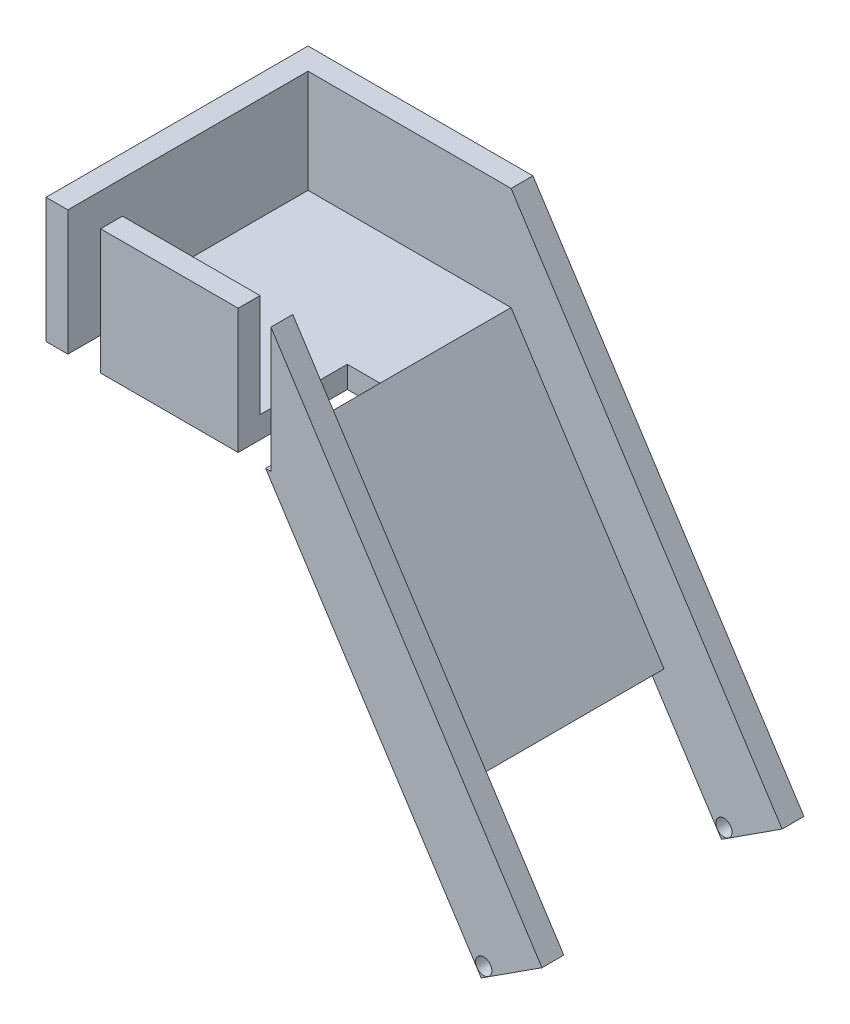
SolidWorks part; units mm, degrees
ref_plane "Plan de face" through (0, 0, 0) normal (0, 0, 1) x (1, 0, 0)
ref_plane "Plan de dessus" through (0, 0, 0) normal (0, 1, 0) x (1, 0, 0)
ref_plane "Plan de droite" through (0, 0, 0) normal (1, 0, 0) x (0, 0, -1)
sketch "Esquisse1" plane through (0, 0, 0) normal (0, 0, 1) x (1, 0, 0)
  line L0 (-33.5313, 99.7152) -> (69.0793, -59.0049)
  line L1 (-136.5313, 99.7152) -> (-33.5313, 99.7152)
  line L2 (-136.5313, 99.7152) -> (-136.5313, 89.7152)
  line L3 (-136.5313, 89.7152) -> (-35.9456, 89.7152)
  line L5 (69.0793, -59.0049) -> (62.8173, -63.0532)
  line L6 (62.8173, -63.0532) -> (-35.9456, 89.7152)
  dimension "D1" = 10
  dimension "D2" = 103
  dimension "D3" = 189
  dimension "D4" = 7.4566
extrude "Boss.-Extru.1" add sketch "Esquisse1" against normal blind 120
sketch "Esquisse3" plane through (0, 99.7152, 0) normal (0, 1, 0) x (1, 0, 0)
  line L0 (-33.5313, 110) -> (-33.5313, 120)
  line L1 (-33.5313, 120) -> (-33.5313, 0) construction
  line L2 (-33.5313, 120) -> (-136.5313, 120)
  line L3 (-136.5313, 120) -> (-136.5313, 0)
  line L4 (-136.5313, 0) -> (-33.5313, 0)
  line L5 (-33.5313, 0) -> (-33.5313, 10)
  line L6 (-33.5313, 10) -> (-126.5313, 10)
  line L7 (-126.5313, 10) -> (-126.5313, 110)
  line L8 (-126.5313, 110) -> (-33.5313, 110)
  dimension "D1" = 10
  dimension "D2" = 10
  dimension "D3" = 10
extrude "Boss.-Extru.3" add sketch "Esquisse3" along normal blind 47.25
sketch "Esquisse4" plane through (0, 0, 0) normal (0, 0, 1) x (1, 0, 0)
  line L0 (-33.5313, 146.9652) -> (90.6221, -45.0777)
  line L1 (90.6221, -45.0777) -> (69.0793, -59.0049)
  line L2 (69.0793, -59.0049) -> (-33.5313, 99.7152)
  line L3 (-33.5313, 99.7152) -> (-33.5313, 146.9652)
  line L4 (62.8173, -63.0532) -> (69.0793, -59.0049) construction
extrude "Boss.-Extru.4" add sketch "Esquisse4" against normal blind 10
sketch "Esquisse5" plane through (0, 0, -120) normal (0, 0, -1) x (-1, 0, 0)
  line L0 (33.5313, 99.7152) -> (33.5313, 146.9652)
  line L1 (33.5313, 146.9652) -> (-90.6221, -45.0777)
  line L2 (-90.6221, -45.0777) -> (-69.0793, -59.0049)
  line L3 (-69.0793, -59.0049) -> (33.5313, 99.7152)
extrude "Boss.-Extru.5" add sketch "Esquisse5" against normal blind 10
sketch "Esquisse6" plane through (0, 0, 0) normal (0, 0, 1) x (1, 0, 0)
  line L0 (-126.5313, 146.9652) -> (-111.5313, 146.9652)
  line L1 (-136.5313, 146.9652) -> (-33.5313, 146.9652) construction
  line L2 (-111.5313, 146.9652) -> (-111.5313, 89.7152)
  line L3 (-136.5313, 89.7152) -> (-35.9456, 89.7152) construction
  line L4 (-111.5313, 89.7152) -> (-126.5313, 89.7152)
  line L5 (-126.5313, 89.7152) -> (-126.5313, 146.9652)
  line L6 (-33.5313, 89.7152) -> (-33.5313, 146.9652)
  line L7 (-33.5313, 146.9652) -> (-48.5313, 146.9652)
  line L8 (-48.5313, 146.9652) -> (-48.5313, 89.7152)
  line L9 (-48.5313, 89.7152) -> (-33.5313, 89.7152)
  line L10 (-136.5313, 146.9652) -> (-136.5313, 89.7152) construction
  dimension "D1" = 15
  dimension "D2" = 15
  dimension "D3" = 10
  dimension "D4" = 63
extrude "Enlèv. mat.-Extru.1" cut sketch "Esquisse6" against normal blind 50
sketch "Esquisse7" plane through (21.8156, 14.1035, 0) normal (0.8398, 0.5429, 0) x (0, 0, -1)
  line L1 (10, -87.0557) -> (110, -87.0557)
  line L2 (10, -87.0557) -> (10, -27.0557)
  line L3 (10, -27.0557) -> (110, -27.0557)
  line L4 (110, -87.0557) -> (110, -27.0557)
  dimension "D1" = 60
extrude "Enlèv. mat.-Extru.2" cut sketch "Esquisse7" against normal blind 10
sketch "Esquisse8" plane through (0, 0, -110) normal (0, 0, 1) x (1, 0, 0)
  circle A0 centre (63.9423, -57.8138) radius 3.73
  dimension "D1" = 7.46
extrude "Enlèv. mat.-Extru.3" cut sketch "Esquisse8" against normal blind 10 and the other way up to next
